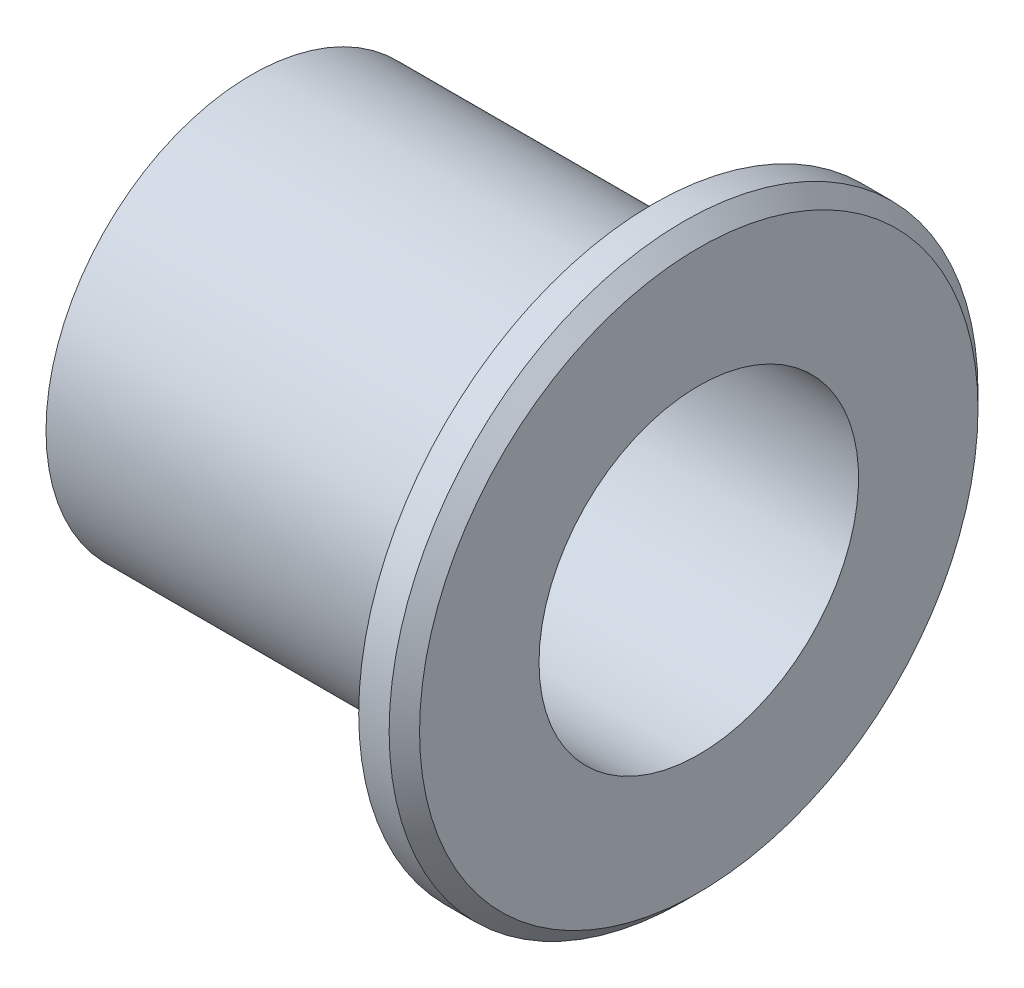
SolidWorks part; units mm, degrees
material "铸造碳钢"
ref_plane "前视基准面" through (0, 0, 0) normal (0, 0, 1) x (1, 0, 0)
ref_plane "上视基准面" through (0, 0, 0) normal (0, 1, 0) x (1, 0, 0)
ref_plane "右视基准面" through (0, 0, 0) normal (1, 0, 0) x (0, 0, -1)
sketch "草图1" plane through (0, 0, 0) normal (0, 0, 1) x (1, 0, 0)
  line L0 (0, 0) -> (8, 0) construction
  line L1 (29.4, 19.35) -> (29.4, 10.5)
  line L2 (29.4, 19.35) -> (26.4, 19.35)
  line L3 (26.4, 19.35) -> (26.4, 12.5)
  line L4 (26.4, 12.5) -> (24.5, 12.5)
  line L5 (24.5, 12.5) -> (24.5, 13.5)
  line L6 (24.5, 13.5) -> (0, 13.5)
  line L7 (0, 13.5) -> (0, 0)
  line L8 (0, 0) -> (8, 0)
  line L9 (29.4, 10.5) -> (8, 10.5)
  line L10 (8, 10.5) -> (8, 0)
  line L11 (21.0645, 0) -> (24.7, 0) construction
  dimension "D1" = 3
  dimension "D2" = 1.9
  dimension "D3" = 24.5
  dimension "D4" = 27
  dimension "D5" = 1
  dimension "D6" = 38.7
  dimension "D7" = 8
  dimension "D8" = 21
revolve "旋转1" add sketch "草图1" angle 360 about L0
cosmetic thread "装饰螺纹线1" parameters "D2"=26
sketch "草图2" plane through (29.4, 0, 0) normal (1, 0, 0) x (0, 0, -1)
  line L1 (-2.3094, 4) -> (-4.6188, 0)
  line L2 (-4.6188, 0) -> (-2.3094, -4)
  line L3 (-2.3094, -4) -> (2.3094, -4)
  line L4 (2.3094, -4) -> (4.6188, 0)
  line L5 (4.6188, 0) -> (2.3094, 4)
  line L6 (2.3094, 4) -> (-2.3094, 4)
  circle A0 centre (0, 0) radius 4 construction
  dimension "D1" = 8
extrude "切除-拉伸1" cut sketch "草图2" against normal through all
chamfer "倒角1" distance 1 angle 45 1 edges at (29.4, 0, 19.35)
sketch "草图3" plane through (29.4, 0, 0) normal (1, 0, 0) x (0, 0, -1)
  circle A0 centre (0, 0) radius 7 construction
  circle A1 centre (0, 7) radius 1.25
  circle A2 centre (0, -7) radius 1.25
  dimension "D1" = 14
  dimension "D2" = 2.5
  dimension "D3" = 2
extrude "切除-拉伸2" cut sketch "草图3" against normal through all
cosmetic thread "装饰螺纹线2" parameters "D2"=3
cosmetic thread "装饰螺纹线3" parameters "D2"=3
move or copy body "实体-移动/复制1" [suppressed] bodies to move or copy 108
